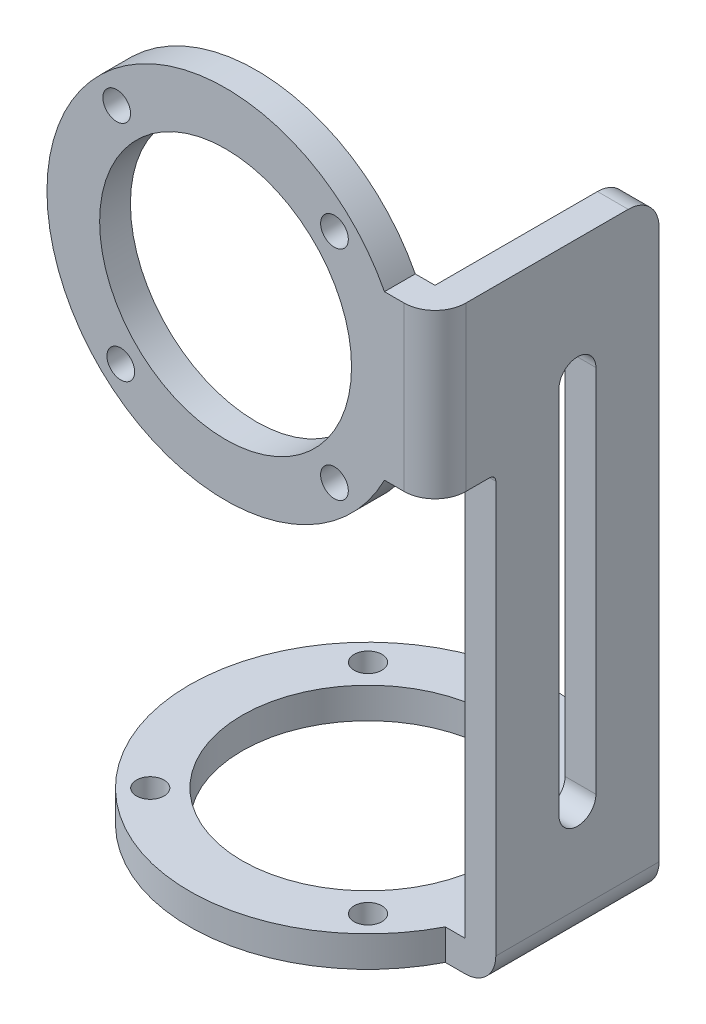
SolidWorks part; units mm, degrees
material "Wrought Stainless Steel"
ref_plane "Front Plane" through (0, 0, 0) normal (0, 0, 1) x (1, 0, 0)
ref_plane "Top Plane" through (0, 0, 0) normal (0, 1, 0) x (1, 0, 0)
ref_plane "Right Plane" through (0, 0, 0) normal (1, 0, 0) x (0, 0, -1)
sketch "Sketch1" plane through (0, 0, 0) normal (0, 0, 1) x (1, 0, 0)
  line L0 (29, 28.1725) -> (29, -28.1725) construction
  line L1 (0, 13.25) -> (29, 13.25)
  line L2 (0, -13.25) -> (29, -13.25)
  circle A0 centre (0, 0) radius 29
  circle A1 centre (0, 0) radius 20.45
  circle A2 centre (0, 0) radius 13.25
  point P8 (29, 0)
  point P11 (0, 13.25)
  point P14 (0, -13.25)
extrude "Boss-Extrude2" add sketch "Sketch1" along normal blind 5 contours A1 L1 A0 L2 | A1 L2 A0 L1 | L0 L1 A0 | L0 A0 L2 | A2
sketch "Sketch2" plane through (29, 0, 0) normal (1, 0, 0) x (0, 0, -1)
  line L0 (0, 13.25) -> (26.375, 13.25)
  line L1 (0, -13.25) -> (31.375, -13.25)
  line L3 (0, 13.25) -> (0, -13.25)
  line L4 (0, -13.25) -> (0, -81)
  line L6 (0, -81) -> (31.375, -81)
  line L7 (31.375, 8.25) -> (31.375, -81)
  arc A1 (26.375, 13.25) -> (31.375, 8.25) centre (26.375, 8.25) cw
  dimension "D1" = 5
extrude "Boss-Extrude3" add sketch "Sketch2" along normal blind 5 separate body contours L4 L6 L7 A1 L0 L3
sketch "Sketch14" plane through (0, -81, 0) normal (0, -1, 0) x (1, 0, 0)
  line L3 (29, 13.2074) -> (29, -49.4574) construction
  line L4 (0, -4.875) -> (29, -4.875)
  line L5 (0, -31.375) -> (29, -31.375)
  circle A3 centre (0, -18.125) radius 29
  circle A4 centre (0, -18.125) radius 20.45
  circle A5 centre (0, -18.125) radius 13.25
  point P16 (29, -18.125)
  line M7 (29, 0) -> (29, -31.375)
extrude "Boss-Extrude6" add sketch "Sketch14" along normal blind 5 separate body contours A4 L5 A3 L4 | A4 L4 A3 L5 | A3 L4 M7 | A3 L5 M7 | A5
sketch "Sketch17" plane through (34, 0, 0) normal (1, 0, 0) x (0, 0, -1)
  line L0 (0, -13.25) -> (3.875, -13.25)
  line L1 (4.875, -81) -> (4.875, -14.25)
  line L2 (0, -13.25) -> (0, -81)
  line L3 (4.875, -81) -> (0, -81)
  arc A0 (4.875, -14.25) -> (3.875, -13.25) centre (3.875, -14.25) ccw
  dimension "D1" = 1
extrude "Cut-Extrude2" cut sketch "Sketch17" against normal blind 5 contours L1 A0 L0 L2 L3
sketch "Sketch21" plane through (0, 13.25, 0) normal (0, 1, 0) x (1, 0, 0)
  line L0 (29, 0) -> (34, 0)
  line L1 (34, 0) -> (29, 0) construction
  line L2 (34, 0) -> (34, 26.375) construction
  line L3 (29, 0) -> (29, -5)
  arc A0 (29, -5) -> (34, 0) centre (29, 0) ccw
  line M2 (29, 0) -> (34, 0)
extrude "Boss-Extrude7" add sketch "Sketch21" against normal blind 26.5 contours L3 A0 M2
sketch "Sketch22" plane through (0, 0, -4.875) normal (0, 0, 1) x (1, 0, 0)
  line L0 (29, -81) -> (29, -86)
  line L1 (29, -86) -> (29, -81) construction
  line L2 (29, -81) -> (34, -81)
  arc A0 (29, -86) -> (34, -81) centre (29, -81) ccw
  line M4 (29, -86) -> (29, -81)
extrude "Boss-Extrude8" add sketch "Sketch22" against normal blind 26.5 contours A0 L2 M4
sketch "Sketch23" plane through (34, 0, 0) normal (1, 0, 0) x (0, 0, -1)
  line L0 (15.125, -36.375) -> (21.125, -36.375)
  line L2 (18.125, -81) -> (18.125, -36.375) construction
  line L3 (31.375, -81) -> (4.875, -81) construction
  line L4 (21.125, -6.375) -> (21.125, -66.375)
  line L5 (15.125, -6.375) -> (15.125, -66.375)
  arc A0 (21.125, -66.375) -> (15.125, -66.375) centre (18.125, -66.375) cw
  arc A1 (21.125, -6.375) -> (15.125, -6.375) centre (18.125, -6.375) ccw
  point P3 (18.125, -36.375)
  point P10 (21.125, -36.375)
  point P13 (15.125, -36.375)
extrude "Cut-Extrude3" cut sketch "Sketch23" against normal blind 26.5 contours L4 A1 L5 L0 | L2 A0 L4 L0 | A0 L2 L0 L5
sketch "Sketch24" plane through (0, 0, 5) normal (0, 0, 1) x (1, 0, 0)
  line L0 (0, 0) -> (17.6777, 17.6777)
  line L1 (0, 0) -> (17.6777, -17.6777)
  line L2 (0, 0) -> (-17.6777, 17.6777)
  line L3 (0, 0) -> (-17.6777, -17.6777)
  circle A0 centre (0, 0) radius 25
  circle A1 centre (17.6777, 17.6777) radius 2.25
  circle A2 centre (17.6777, -17.6777) radius 2.25
  circle A3 centre (-17.6777, 17.6777) radius 2.25
  circle A4 centre (-17.0153, -18.3161) radius 2.25
extrude "Cut-Extrude5" cut sketch "Sketch24" against normal blind 10 contours A4 | A3 | A1 | A2
sketch "Sketch25" plane through (0, -86, 0) normal (0, -1, 0) x (1, 0, 0)
  line L0 (0, -18.125) -> (17.6777, -0.4473)
  line L1 (0, -18.125) -> (17.6777, -35.8027)
  line L2 (0, -18.125) -> (-17.6777, -35.8027)
  line L3 (0, -18.125) -> (-17.6777, -0.4473)
  circle A0 centre (0, -18.125) radius 25
  circle A1 centre (-17.6777, -0.4473) radius 2.25
  circle A2 centre (17.6777, -0.4473) radius 2.25
  circle A3 centre (17.6777, -35.8027) radius 2.25
  circle A4 centre (-17.6777, -35.8027) radius 2.25
extrude "Cut-Extrude6" cut sketch "Sketch25" against normal blind 10 contours A1 | A2 | A3 | A4
